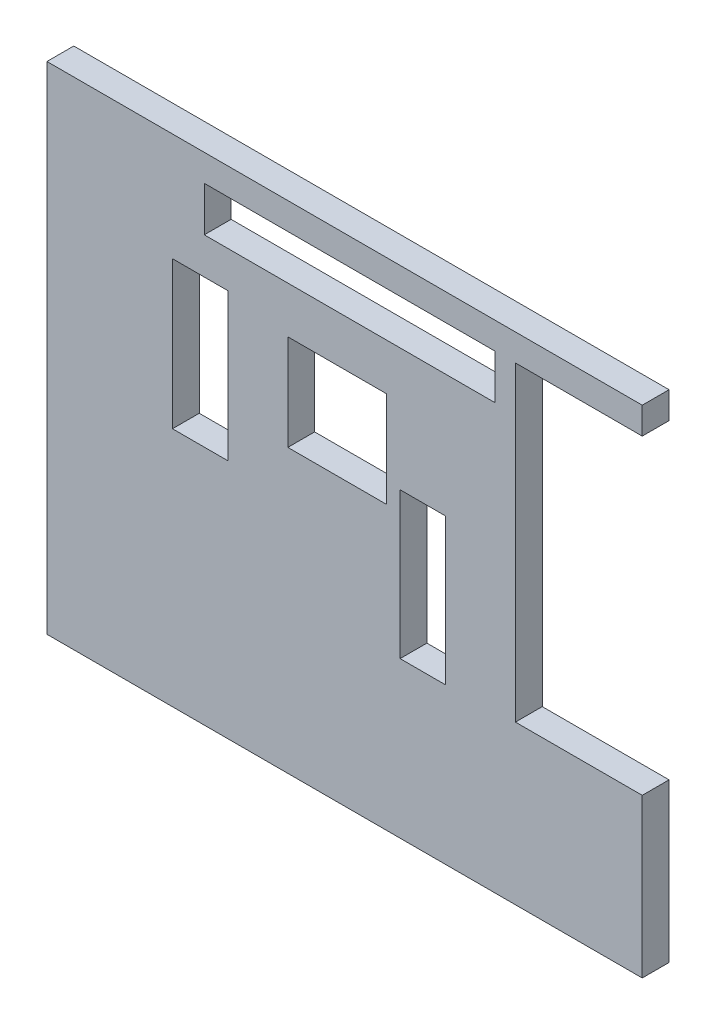
SolidWorks part; units mm, degrees
ref_plane "Alzado" through (0, 0, 0) normal (0, 0, 1) x (1, 0, 0)
ref_plane "Planta" through (0, 0, 0) normal (0, 1, 0) x (1, 0, 0)
ref_plane "Vista lateral" through (0, 0, 0) normal (1, 0, 0) x (0, 0, -1)
sketch "Croquis1" plane through (0, 0, 0) normal (0, 0, 1) x (1, 0, 0)
  line L0 (29.8896, 86.8319) -> (84.0931, 86.8319)
  line L1 (29.8896, 86.8319) -> (29.8896, 78.5078)
  line L2 (29.8896, 78.5078) -> (84.0931, 78.5078)
  line L3 (0.5536, 91.8319) -> (0.5536, 5.3319)
  line L4 (0.5536, 5.3319) -> (111.5536, 5.3319)
  line L5 (111.5536, 5.3319) -> (111.5536, 28.8319)
  line L6 (111.5536, 91.8319) -> (0.5536, 91.8319)
  line L7 (84.0931, 86.8319) -> (84.0931, 78.5078)
  line L8 (23.9606, 71.6891) -> (34.3307, 71.6891)
  line L9 (23.9606, 71.6891) -> (23.9606, 44.2276)
  line L10 (23.9606, 44.2276) -> (34.3307, 44.2276)
  line L11 (34.3307, 71.6891) -> (34.3307, 44.2276)
  line L12 (66.4011, 55.6014) -> (74.8508, 55.6014)
  line L13 (66.4011, 55.6014) -> (66.4011, 28.3319)
  line L14 (66.4011, 28.3319) -> (74.8508, 28.3319)
  line L15 (74.8508, 55.6014) -> (74.8508, 28.3319)
  line L16 (45.4689, 69.8319) -> (63.9046, 69.8319)
  line L17 (45.4689, 69.8319) -> (45.4689, 51.9723)
  line L18 (45.4689, 51.9723) -> (63.9046, 51.9723)
  line L19 (63.9046, 69.8319) -> (63.9046, 51.9723)
  line L20 (87.9095, 86.8319) -> (111.5536, 86.8319)
  line L21 (87.9095, 86.8319) -> (87.9095, 28.8319)
  line L22 (87.9095, 28.8319) -> (111.5536, 28.8319)
  line L24 (111.5536, 86.8319) -> (111.5536, 91.8319)
  dimension "D1" = 111
  dimension "D2" = 86.5
  dimension "D3" = 23.6441
  dimension "D4" = 58
  dimension "D5" = 10.3701
  dimension "D6" = 27.4615
  dimension "D7" = 18.4357
  dimension "D8" = 17.8596
  dimension "D9" = 8.4497
  dimension "D10" = 27.2695
  dimension "D11" = 54.2036
  dimension "D12" = 8.3241
  dimension "D13" = 29.336
  dimension "D14" = 5
  dimension "D15" = 23.407
  dimension "D16" = 20.1428
  dimension "D17" = 44.9154
  dimension "D18" = 22
  dimension "D19" = 65.8476
  dimension "D20" = 23
  dimension "D21" = 0.5536
  dimension "D22" = 28.3319
extrude "Saliente-Extruir1" add sketch "Croquis1" along normal blind 5
sketch "Croquis2" plane through (0, 0, 5) normal (0, 0, 1) x (1, 0, 0)
  line L0 (23.9606, 44.2276) -> (34.3307, 44.2276) construction
  line L1 (34.3307, 71.6891) -> (23.9606, 71.6891) construction
  line L2 (23.9606, 71.6891) -> (23.9606, 44.2276) construction
  line L3 (34.3307, 44.2276) -> (34.3307, 71.6891) construction
  line L4 (45.4689, 69.8319) -> (45.4689, 51.9723) construction
  line L5 (63.9046, 69.8319) -> (45.4689, 69.8319) construction
  line L6 (63.9046, 51.9723) -> (63.9046, 69.8319) construction
  line L7 (45.4689, 51.9723) -> (63.9046, 51.9723) construction
  line L8 (111.5536, 91.8319) -> (0.5536, 91.8319)
  line L9 (0.5536, 91.8319) -> (0.5536, 5.3319)
  line L10 (0.5536, 5.3319) -> (111.5536, 5.3319)
  line L11 (111.5536, 5.3319) -> (111.5536, 28.8319)
  line L12 (111.5536, 28.8319) -> (87.9095, 28.8319)
  line L13 (87.9095, 28.8319) -> (87.9095, 86.8319)
  line L14 (87.9095, 86.8319) -> (111.5536, 86.8319)
  line L15 (111.5536, 86.8319) -> (111.5536, 91.8319)
  line L16 (111.5536, 91.8319) -> (0.5536, 91.8319)
  line L17 (0.5536, 91.8319) -> (0.5536, 5.3319)
  line L18 (0.5536, 5.3319) -> (111.5536, 5.3319)
  line L19 (111.5536, 5.3319) -> (111.5536, 28.8319)
  line L20 (111.5536, 28.8319) -> (87.9095, 28.8319)
  line L21 (87.9095, 28.8319) -> (87.9095, 86.8319)
  line L22 (87.9095, 86.8319) -> (111.5536, 86.8319)
  line L23 (111.5536, 86.8319) -> (111.5536, 91.8319)
  line L24 (66.4011, 28.3319) -> (74.8508, 28.3319) construction
  line L25 (74.8508, 28.3319) -> (74.8508, 55.6014) construction
  line L26 (66.4011, 55.6014) -> (66.4011, 28.3319) construction
  line L27 (74.8508, 55.6014) -> (66.4011, 55.6014) construction
  line L28 (84.0931, 78.5078) -> (84.0931, 86.8319) construction
  line L29 (29.8896, 86.8319) -> (29.8896, 78.5078) construction
  line L30 (84.0931, 86.8319) -> (29.8896, 86.8319) construction
  line L31 (29.8896, 78.5078) -> (84.0931, 78.5078) construction
  line L32 (23.9606, 44.2276) -> (34.3307, 44.2276)
  line L33 (34.3307, 71.6891) -> (23.9606, 71.6891)
  line L34 (23.9606, 71.6891) -> (23.9606, 44.2276)
  line L35 (34.3307, 44.2276) -> (34.3307, 71.6891)
  line L36 (45.4689, 69.8319) -> (45.4689, 51.9723)
  line L37 (63.9046, 69.8319) -> (45.4689, 69.8319)
  line L38 (63.9046, 51.9723) -> (63.9046, 69.8319)
  line L39 (45.4689, 51.9723) -> (63.9046, 51.9723)
  line L40 (66.4011, 28.3319) -> (74.8508, 28.3319)
  line L41 (74.8508, 28.3319) -> (74.8508, 55.6014)
  line L42 (66.4011, 55.6014) -> (66.4011, 28.3319)
  line L43 (74.8508, 55.6014) -> (66.4011, 55.6014)
  line L44 (84.0931, 78.5078) -> (84.0931, 86.8319)
  line L45 (29.8896, 86.8319) -> (29.8896, 78.5078)
  line L46 (84.0931, 86.8319) -> (29.8896, 86.8319)
  line L47 (29.8896, 78.5078) -> (84.0931, 78.5078)
  dimension "D1" = 0
sketch "Croquis3" plane through (0, 5.3319, 0) normal (0, -1, 0) x (1, 0, 0)
  line L4 (0.5536, 0) -> (111.5536, 0)
  line L5 (111.5536, 0) -> (111.5536, 5)
  line L6 (111.5536, 5) -> (0.5536, 5)
  line L7 (0.5536, 5) -> (0.5536, 0)
  line L8 (0.5536, 0) -> (111.5536, 0)
  line L9 (111.5536, 0) -> (111.5536, 5)
  line L10 (111.5536, 5) -> (0.5536, 5)
  line L11 (0.5536, 5) -> (0.5536, 0)
  dimension "D1" = 0
extrude "Saliente-Extruir2" add sketch "Croquis3" along normal blind 6
